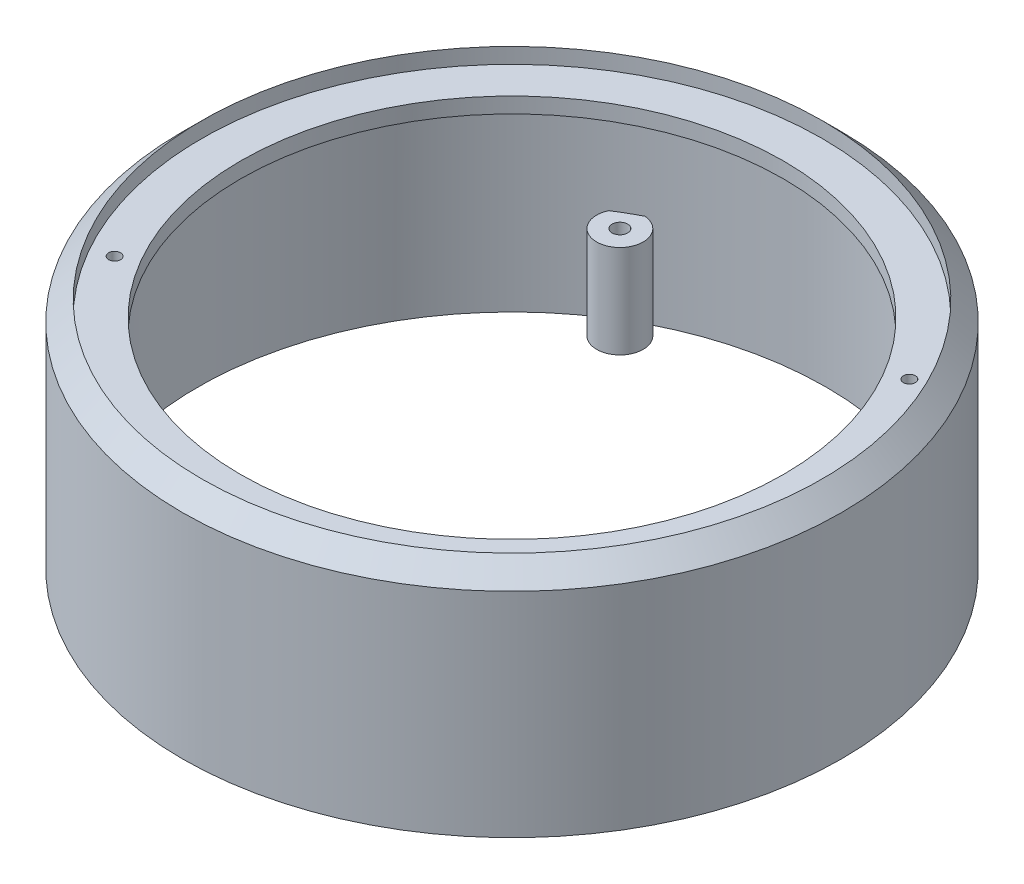
SolidWorks part; units mm, degrees
ref_plane "Front Plane" through (0, 0, 0) normal (0, 0, 1) x (1, 0, 0)
ref_plane "Top Plane" through (0, 0, 0) normal (0, 1, 0) x (1, 0, 0)
ref_plane "Right Plane" through (0, 0, 0) normal (1, 0, 0) x (0, 0, -1)
sketch "Sketch1" plane through (0, 0, 0) normal (0, 0, 1) x (1, 0, 0)
  line L0 (0, -62.4635) -> (0, 62.4635) construction
  line L1 (-85, 0) -> (-85, 55)
  line L2 (-85, 55) -> (-80, 60)
  line L3 (-85, 0) -> (-81, 0)
  line L4 (-81, 0) -> (-81, 52)
  line L5 (-81, 52) -> (-70, 52)
  line L6 (-70, 52) -> (-70, 56)
  line L7 (-70, 56) -> (-80, 56)
  line L8 (-80, 56) -> (-80, 60)
  point P4 (0, 0)
  dimension "D1" = 85
  dimension "D2" = 4
  dimension "D4" = 135
  dimension "D5" = 60
  dimension "D6" = 10
  dimension "D7" = 4
  dimension "D8" = 4
  dimension "85" = 55
revolve "Revolve1" add sketch "Sketch1" angle 360 about L0
sketch "Sketch2" plane through (0, 0, 0) normal (0, -1, 0) x (1, 0, 0)
  circle A0 centre (76, 0) radius 2
  arc A2 (80.9276, 3.4232) -> (80.9276, -3.4232) centre (76, 0) ccw
  circle A3 centre (0, 0) radius 81 construction
  arc A4 (80.9276, -3.4232) -> (80.9276, 3.4232) centre (0, 0) ccw
  circle A5 centre (76, 0) radius 6 construction
  circle A6 centre (-38, -65.8179) radius 2
  arc A7 (-37.4992, -71.797) -> (-43.4284, -68.3738) centre (-38, -65.8179) ccw
  circle A8 centre (-38, 65.8179) radius 2
  arc A9 (-43.4284, 68.3738) -> (-37.4992, 71.797) centre (-38, 65.8179) ccw
  arc A10 (-43.4284, -68.3738) -> (-37.4992, -71.797) centre (0, 0) ccw
  arc A11 (-37.4992, 71.797) -> (-43.4284, 68.3738) centre (0, 0) ccw
  arc A12 (80.9276, -3.4232) -> (80.9276, 3.4232) centre (0, 0) ccw
  circle M1 centre (0, 0) radius 81
  dimension "D1" = 4
  dimension "D2" = 76
  dimension "D3" = 4
  dimension "D4" = 3
extrude "Boss-Extrude1" add sketch "Sketch2" against normal blind 24 contours A9 A8 M1 | A7 A6 M1 | A2 A0 M1
sketch "Sketch3" plane through (0, 56, 0) normal (0, 1, 0) x (1, 0, 0)
  circle A0 centre (-64.9519, -37.5) radius 1.55 construction
  circle A1 centre (-64.9519, -37.5) radius 1.55
  circle A2 centre (64.9519, 37.5) radius 1.55 construction
  circle A3 centre (64.9519, 37.5) radius 1.55
extrude "Cut-Extrude1" cut sketch "Sketch3" against normal blind 10
